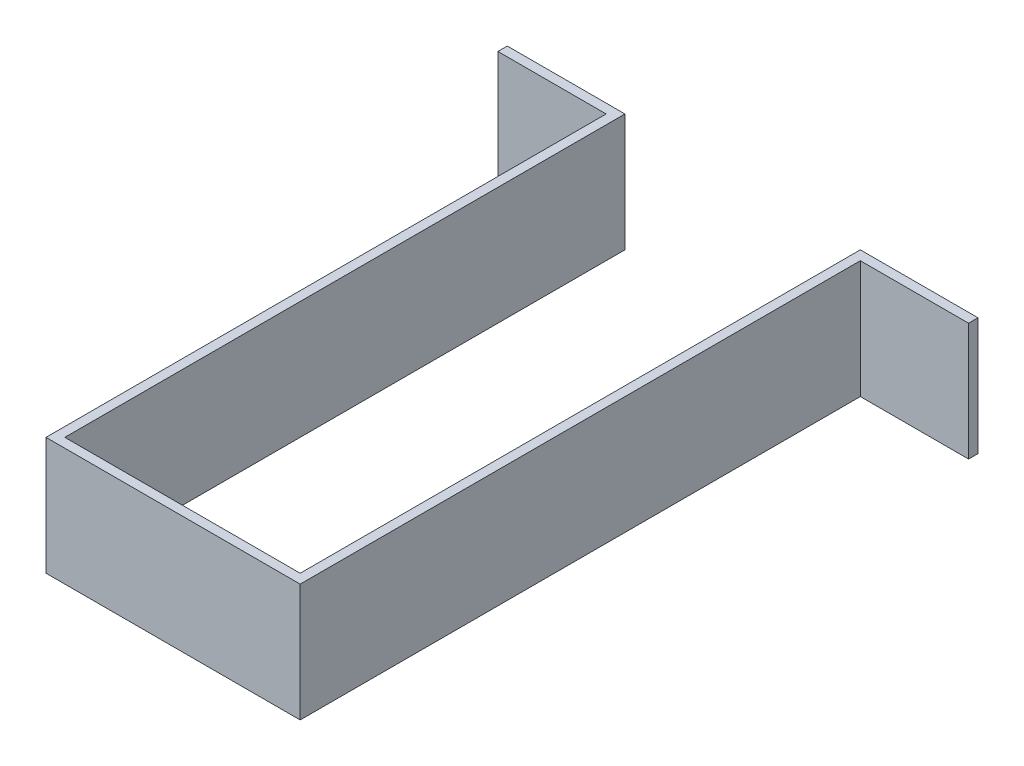
SolidWorks part; units mm, degrees
ref_plane "Front Plane" through (0, 0, 0) normal (0, 0, 1) x (1, 0, 0)
ref_plane "Top Plane" through (0, 0, 0) normal (0, 1, 0) x (1, 0, 0)
ref_plane "Right Plane" through (0, 0, 0) normal (1, 0, 0) x (0, 0, -1)
sketch "Sketch2" plane through (0, 0, 0) normal (0, 1, 0) x (1, 0, 0)
  line L0 (0, 0) -> (0, 119)
  line L1 (0, 0) -> (50, 0)
  line L2 (50, 0) -> (50, 119)
  line L3 (0, 119) -> (-25, 119)
  line L4 (50, 119) -> (75, 119)
  line L5 (-25, 119) -> (-25, 117)
  line L6 (-25, 117) -> (-2, 117)
  line L7 (-2, 117) -> (-2, -2)
  line L8 (-2, -2) -> (52, -2)
  line L9 (52, -2) -> (52, 117)
  line L10 (52, 117) -> (75, 117)
  line L11 (75, 117) -> (75, 119)
  dimension "D1" = 50
  dimension "D2" = 119
  dimension "D3" = 119
  dimension "D4" = 25
  dimension "D5" = 25
  dimension "D6" = 2
  dimension "D7" = 2
  dimension "D8" = 2
  dimension "D9" = 2
  dimension "D10" = 2
extrude "Boss-Extrude1" add sketch "Sketch2" against normal blind 25
